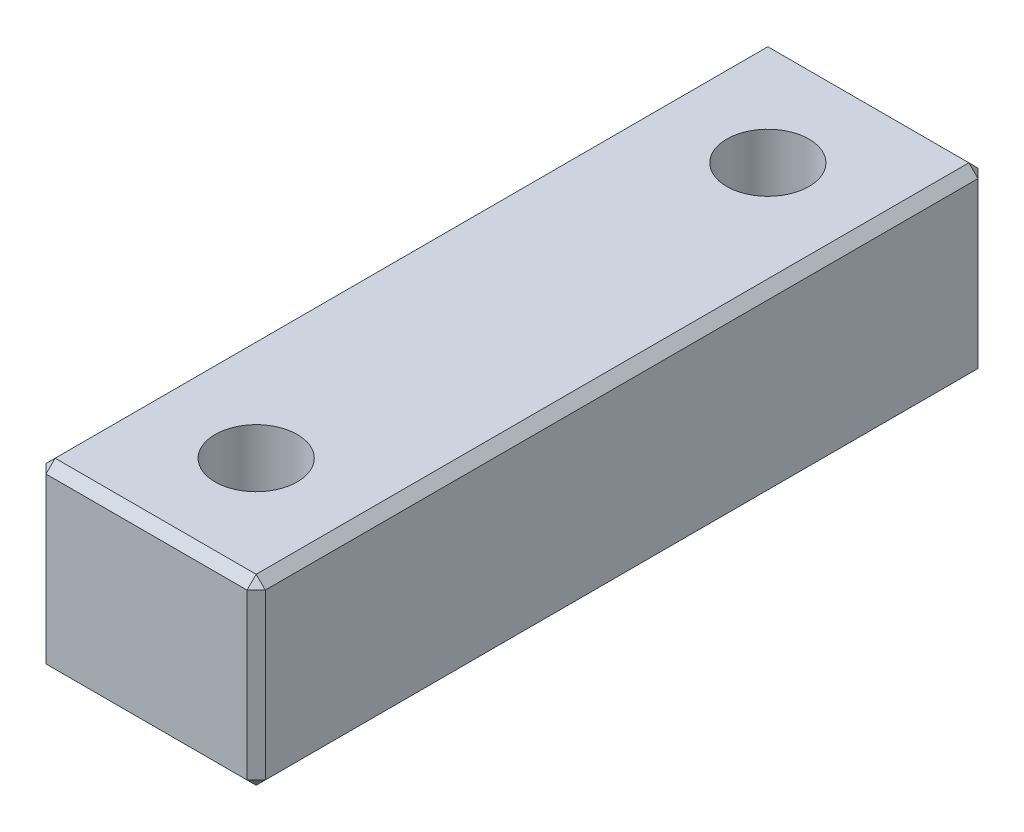
SolidWorks part; units mm, degrees
ref_plane "Alzado" through (0, 0, 0) normal (0, 0, 1) x (1, 0, 0)
ref_plane "Planta" through (0, 0, 0) normal (0, 1, 0) x (1, 0, 0)
ref_plane "Vista lateral" through (0, 0, 0) normal (1, 0, 0) x (0, 0, -1)
sketch "Croquis1" plane through (0, 0, 0) normal (0, 0, 1) x (1, 0, 0)
  line L1 (6, -5) -> (-6, -5)
  line L2 (6, -5) -> (6, 5)
  line L3 (6, 5) -> (-6, 5)
  line L4 (-6, -5) -> (-6, 5)
  line L5 (6, -5) -> (-6, 5) construction
  line L6 (6, 5) -> (-6, -5) construction
  point P0 (0, 0)
  dimension "D1" = 10
  dimension "D2" = 12
extrude "Saliente-Extruir1" add sketch "Croquis1" along normal mid plane 40
ref_plane "Plano1" through (0, 0, -14) normal (0, 0, 1) x (1, 0, 0)
sketch "Croquis3" plane through (0, 0, -14) normal (0, 0, 1) x (1, 0, 0)
  line L0 (0, 5) -> (0, -6.2814) construction
  line L1 (6, 5) -> (-6, 5) construction
  line L2 (0, 5) -> (-2.25, 5)
  line L3 (-2.25, 5) -> (-2.25, -3.2)
  line L4 (-2.25, -3.2) -> (-4, -5)
  line L5 (-6, -5) -> (6, -5) construction
  line L6 (-4, -5) -> (0, -5)
  line L7 (0, -5) -> (0, 5)
  dimension "D1" = 4.5
  dimension "D2" = 8
  dimension "D3" = 1.8
revolve "Cortar-Revolución1" cut sketch "Croquis3" angle 360 about L0
mirror "Simetría1" about plane through (0, 0, 0) normal (0, 0, 1) of "Cortar-Revolución1"
chamfer "Chaflán1" distance 0.5 angle 45 12 edges at (0, -5, -20) (0, 5, -20) (0, 5, 20) (-6, 5, 0) (-6, 0, 20) (-6, 0, -20) (-6, -5, 0) (0, -5, 20) (6, -5, 0) (6, 0, 20) (6, 5, 0) (6, 0, -20)
